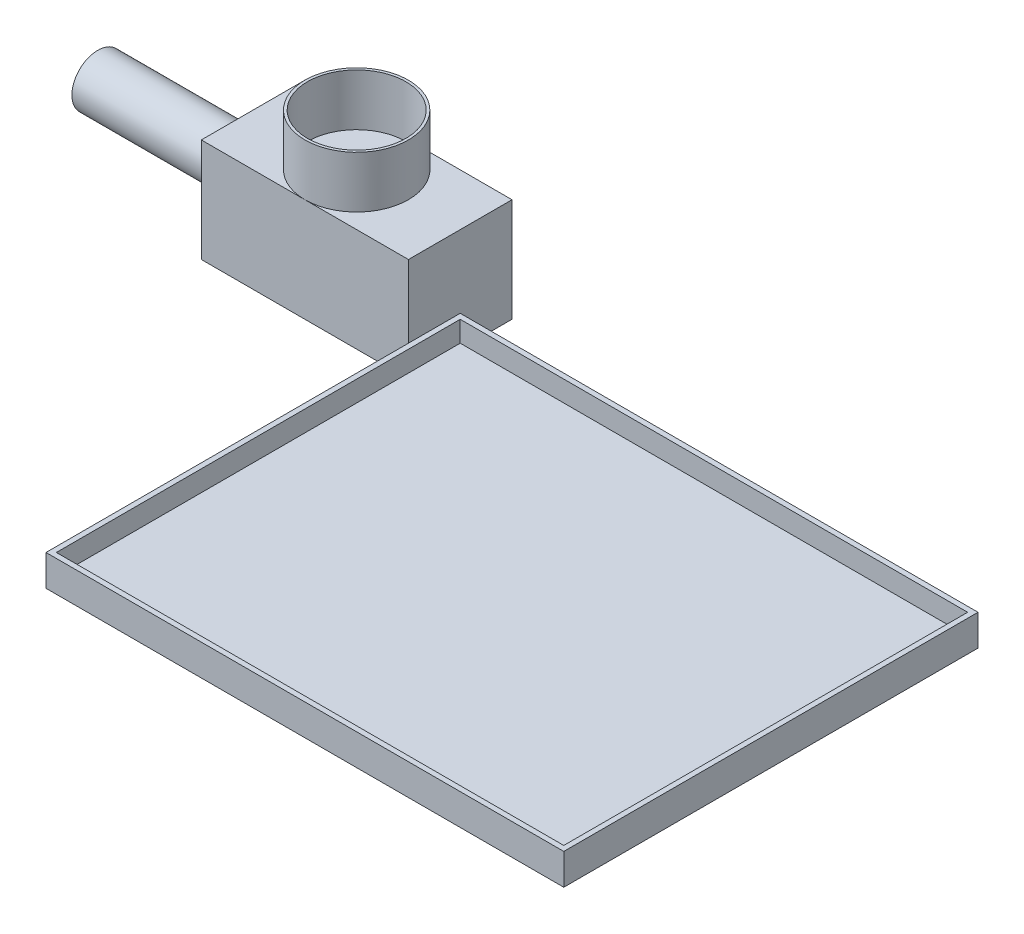
SolidWorks part; units mm, degrees
ref_plane "Front Plane" through (0, 0, 0) normal (0, 0, 1) x (1, 0, 0)
ref_plane "Top Plane" through (0, 0, 0) normal (0, 1, 0) x (1, 0, 0)
ref_plane "Right Plane" through (0, 0, 0) normal (1, 0, 0) x (0, 0, -1)
sketch "Sketch1" plane through (0, 0, 0) normal (1, 0, 0) x (0, 0, -1)
  circle A0 centre (0, 0) radius 25
  dimension "D1" = 50
extrude "Boss-Extrude1" add sketch "Sketch1" along normal blind 150
sketch "Sketch2" plane through (150, 0, 0) normal (1, 0, 0) x (0, 0, -1)
  line L1 (-50, -50) -> (50, -50)
  line L2 (-50, -50) -> (-50, 50)
  line L3 (-50, 50) -> (50, 50)
  line L4 (50, -50) -> (50, 50)
  line L5 (-50, -50) -> (50, 50) construction
  line L6 (-50, 50) -> (50, -50) construction
  point P0 (0, 0)
  dimension "D1" = 100
  dimension "D2" = 100
extrude "Boss-Extrude2" add sketch "Sketch2" along normal blind 200
sketch "Sketch3" plane through (0, 50, 0) normal (0, 1, 0) x (1, 0, 0)
  circle A0 centre (250, 0) radius 50
  circle A1 centre (250, 0) radius 47.5
  dimension "D1" = 95
  dimension "D2" = 100
extrude "Boss-Extrude3" add sketch "Sketch3" along normal blind 50
sketch "Sketch4" plane through (0, -50, 0) normal (0, 1, 0) x (1, 0, 0)
  line L0 (350, 50) -> (350, -50) construction
  line L1 (350, 0) -> (850, 0)
  line L2 (350, 0) -> (350, -400)
  line L3 (350, -400) -> (850, -400)
  line L4 (850, 0) -> (850, -400)
  line L6 (355, -395) -> (845, -395)
  line L7 (355, -395) -> (355, -5)
  line L8 (355, -5) -> (845, -5)
  line L9 (845, -395) -> (845, -5)
  line L10 (355, -395) -> (845, -5) construction
  line L11 (355, -5) -> (845, -395) construction
  point P6 (600, -200)
  dimension "D1" = 500
  dimension "D2" = 400
  dimension "D3" = 390
  dimension "D4" = 490
  dimension "D5" = 200
  dimension "D6" = 250
extrude "Boss-Extrude4" add sketch "Sketch4" along normal blind 30
sketch "Sketch5" plane through (0, -50, 0) normal (0, -1, 0) x (1, 0, 0)
  line L1 (355, 395) -> (845, 395)
  line L2 (355, 395) -> (355, 5)
  line L3 (355, 5) -> (845, 5)
  line L4 (845, 395) -> (845, 5)
extrude "Boss-Extrude5" add sketch "Sketch5" against normal blind 10
